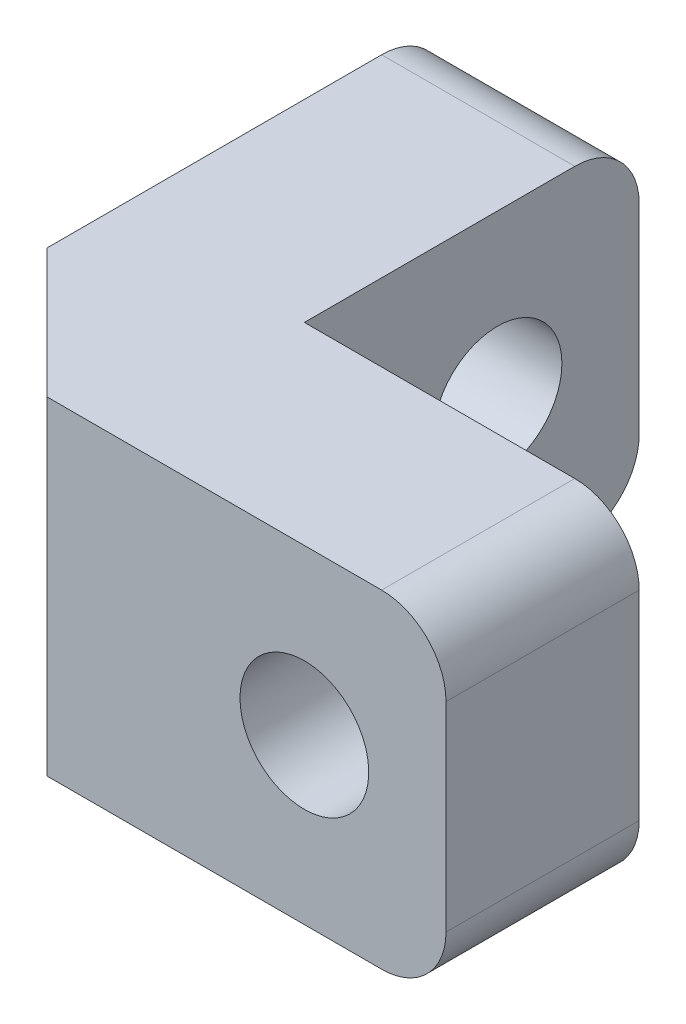
SolidWorks part; units mm, degrees
material "Custom Plastic"
ref_plane "Front Plane" through (0, 0, 0) normal (0, 0, 1) x (1, 0, 0)
ref_plane "Top Plane" through (0, 0, 0) normal (0, 1, 0) x (1, 0, 0)
ref_plane "Right Plane" through (0, 0, 0) normal (1, 0, 0) x (0, 0, -1)
sketch "Sketch1" plane through (0, 0, 0) normal (0, 1, 0) x (1, 0, 0)
  line L0 (0, 0) -> (0, 5.2)
  line L1 (0, 5.2) -> (-3, 5.2)
  line L2 (-3, 5.2) -> (-3, -3)
  line L3 (-3, -3) -> (5.2, -3)
  line L4 (5.2, -3) -> (5.2, 0)
  line L5 (0, 0) -> (5.2, 0)
  dimension "D1" = 5.2
  dimension "D2" = 3
  dimension "D3" = 8.2
  dimension "D4" = 8.2
  dimension "D5" = 3
extrude "Boss-Extrude1" add sketch "Sketch1" along normal blind 5.1
chamfer "Chamfer1" distance 2 angle 45 1 edges at (-3, 2.55, 3)
fillet "Fillet1" radius 1 4 edges at (5.2, 0, 1.5) (5.2, 5.1, 1.5) (-1.5, 0, -5.2) (-1.5, 5.1, -5.2)
sketch "Sketch3" plane through (0, 0, 0) normal (1, 0, 0) x (0, 0, -1)
  line L0 (5.2, 4.1) -> (5.2, 1) construction
  line L1 (0, 5.1) -> (4.2, 5.1) construction
  line L2 (0, 5.1) -> (0, 0) construction
  circle A0 centre (3, 2.55) radius 1
  point P0 (3, 2.55)
  dimension "D3" = 2
  dimension "D1" = 3
  dimension "D2" = 2.55
extrude "Cut-Extrude1" cut sketch "Sketch3" against normal blind 5.1
sketch "Sketch4" plane through (0, 0, 0) normal (0, 0, -1) x (-1, 0, 0)
  line L0 (-4.2, 0) -> (0, 0) construction
  line L1 (0, 5.1) -> (0, 0) construction
  circle A0 centre (-3, 2.55) radius 1
  point P0 (-3, 2.55)
  dimension "D3" = 2
  dimension "D1" = 2.55
  dimension "D2" = 3
extrude "Cut-Extrude2" cut sketch "Sketch4" against normal blind 5.1
sketch "Sketch5" plane through (0, 0, 0) normal (0, 0, -1) x (-1, 0, 0)
  circle A0 centre (-3, 2.55) radius 1.7
  dimension "D1" = 3.4
extrude "Cut-Extrude3" cut sketch "Sketch5" against normal blind 1.4
sketch "Sketch6" plane through (-3, 0, 0) normal (-1, 0, 0) x (0, 0, 1)
  circle A0 centre (-3, 2.55) radius 1.7
  dimension "D1" = 3.4
extrude "Cut-Extrude4" cut sketch "Sketch6" against normal blind 1.4
